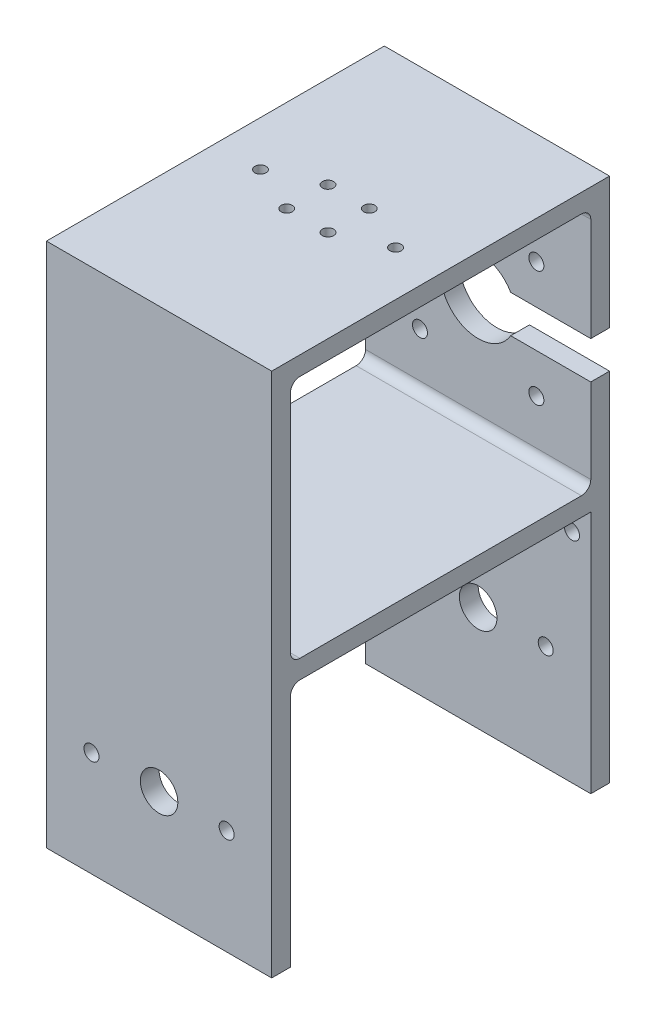
SolidWorks part; units mm, degrees
ref_plane "Front Plane" through (0, 0, 0) normal (0, 0, 1) x (1, 0, 0)
ref_plane "Top Plane" through (0, 0, 0) normal (0, 1, 0) x (1, 0, 0)
ref_plane "Right Plane" through (0, 0, 0) normal (1, 0, 0) x (0, 0, -1)
sketch "Sketch1" plane through (0, 0, 0) normal (1, 0, 0) x (0, 0, -1)
  line L0 (0, 0) -> (0, -140)
  line L1 (0, -140) -> (-5, -140)
  line L2 (-5, -140) -> (-5, -75)
  line L3 (-5, -75) -> (-85, -75)
  line L4 (-85, -75) -> (-85, -140)
  line L5 (-85, -140) -> (-90, -140)
  line L6 (-90, -140) -> (-90, 0)
  line L7 (-90, 0) -> (0, 0)
  dimension "D1" = 90
  dimension "D2" = 80
  dimension "D3" = 5
  dimension "D4" = 80
  dimension "D5" = 65
  dimension "D6" = 65
  dimension "D7" = 75
  dimension "D8" = 140
  dimension "D9" = 5
extrude "Boss-Extrude1" add sketch "Sketch1" against normal blind 60
sketch "Sketch2" plane through (0, 0, 0) normal (1, 0, 0) x (0, 0, -1)
  line L0 (-85, -75) -> (-5, -75) construction
  line L1 (-85, -70) -> (-5, -70)
  line L2 (-85, -70) -> (-85, -5)
  line L3 (-85, -5) -> (-5, -5)
  line L4 (-5, -70) -> (-5, -5)
  line L5 (0, 0) -> (-90, 0) construction
  line L6 (0, -140) -> (0, 0) construction
  line L7 (-90, 0) -> (-90, -140) construction
  dimension "D1" = 5
  dimension "D2" = 5
  dimension "D3" = 5
  dimension "D4" = 5
  dimension "D5" = 65
  dimension "D6" = 80
extrude "Cut-Extrude1" cut sketch "Sketch2" against normal blind 60
sketch "Sketch3" plane through (0, 0, 0) normal (0, 1, 0) x (1, 0, 0)
  line L0 (-30, 0) -> (-30, -90) construction
  line L1 (-60, 0) -> (0, 0) construction
  line L2 (-60, -90) -> (0, -90) construction
  line L3 (-60, -45) -> (0, -45) construction
  line L4 (-60, 0) -> (-60, -90) construction
  line L5 (0, 0) -> (0, -90) construction
  circle A7 centre (-24.5, -50.5) radius 1.5
  circle A8 centre (-35.5, -50.5) radius 1.5
  circle A9 centre (-35.5, -39.5) radius 1.5
  circle A10 centre (-24.5, -39.5) radius 1.5
  circle A11 centre (-12, -45) radius 1.5
  circle A12 centre (-48, -45) radius 1.5
  point P12 (-30, -45)
  dimension "D5" = 3
  dimension "D6" = 3
  dimension "D7" = 3
  dimension "D8" = 3
  dimension "D9" = 3
  dimension "D1" = 11
  dimension "D2" = 11
  dimension "D3" = 12
  dimension "D4" = 12
extrude "Cut-Extrude2" cut sketch "Sketch3" against normal up to next
sketch "Sketch4" plane through (0, 0, 0) normal (0, 0, 1) x (1, 0, 0)
  line L0 (-30, 0) -> (-30, -140) construction
  line L1 (-60, 0) -> (0, 0) construction
  line L2 (-60, -140) -> (0, -140) construction
  line L4 (0, 0) -> (0, -140) construction
  line L5 (-60, 0) -> (-60, -140) construction
  line L6 (-60, -140) -> (0, -140) construction
  line L11 (0, -70) -> (-60, -70) construction
  line L12 (0, -140) -> (0, 0) construction
  line L13 (-60, -140) -> (-60, 0) construction
  line L14 (-30, -40) -> (0, -40) construction
  line L21 (-14.5, -55.5) -> (-45.5, -24.5) construction
  line L22 (-14.5, -24.5) -> (-45.5, -55.5) construction
  line L23 (-60, 0) -> (0, 0) construction
  circle A0 centre (-30, -112) radius 5
  circle A1 centre (-30, -40) radius 10
  circle A6 centre (-5, -82) radius 2
  circle A7 centre (-55, -82) radius 2
  circle A12 centre (-14.5, -24.5) radius 2
  circle A13 centre (-45.5, -24.5) radius 2
  circle A14 centre (-45.5, -55.5) radius 2
  circle A15 centre (-14.5, -55.5) radius 2
  dimension "D2" = 10
  dimension "D3" = 20
  dimension "D7" = 4
  dimension "D8" = 4
  dimension "D9" = 24.5
  dimension "D10" = 4
  dimension "D19" = 4
  dimension "D20" = 4
  dimension "D11" = 4
  dimension "D4" = 72
  dimension "D5" = 31
  dimension "D6" = 31
  dimension "D13" = 12
  dimension "D14" = 12
  dimension "D15" = 28
  dimension "D16" = 58
  dimension "D17" = 5
  dimension "D18" = 5
  dimension "D21" = 58
extrude "Cut-Extrude3" cut sketch "Sketch4" along normal up to next
fillet "Fillet1" radius 2.5 1 edges at (-30, -75, 85)
fillet "Fillet3" radius 2.5 1 edges at (-30, -70, 85)
fillet "Fillet4" radius 2.5 1 edges at (-30, -70, 5)
fillet "Fillet5" radius 2.5 1 edges at (-30, -5, 5)
fillet "Fillet6" radius 2.5 1 edges at (-30, -5, 85)
sketch "Sketch5" plane through (0, 0, 90) normal (0, 0, 1) x (1, 0, 0)
  line L0 (-30, 0) -> (-30, -140) construction
  line L1 (-60, 0) -> (0, 0) construction
  line L2 (-60, -140) -> (0, -140) construction
  circle A0 centre (-30, -112) radius 5
  circle A1 centre (-12, -112) radius 2
  circle A2 centre (-48, -112) radius 2
  dimension "D2" = 10
  dimension "D5" = 4
  dimension "D6" = 4
  dimension "D1" = 28
  dimension "D3" = 18
  dimension "D4" = 18
extrude "Cut-Extrude4" cut sketch "Sketch5" against normal through all
sketch "Sketch6" plane through (0, 0, 0) normal (0, 0, -1) x (-1, 0, 0)
  line L0 (30, -30) -> (30, -50) construction
  line L2 (0, -45) -> (30, -45)
  line L9 (0, -70) -> (60, -70) construction
  line L11 (0, -45) -> (0, -35)
  line L15 (0, -140) -> (0, 0) construction
  line L16 (60, -140) -> (60, 0) construction
  line L17 (20, -40) -> (40, -40) construction
  line L18 (0, -35) -> (30, -35)
  line L19 (30, -45) -> (30, -35)
  circle A2 centre (30, -40) radius 10 construction
  point P2 (30, -40)
  dimension "D1" = 5
  dimension "D2" = 5
  dimension "D3" = 30
  dimension "D4" = 10
extrude "Cut-Extrude5" cut sketch "Sketch6" against normal up to next
